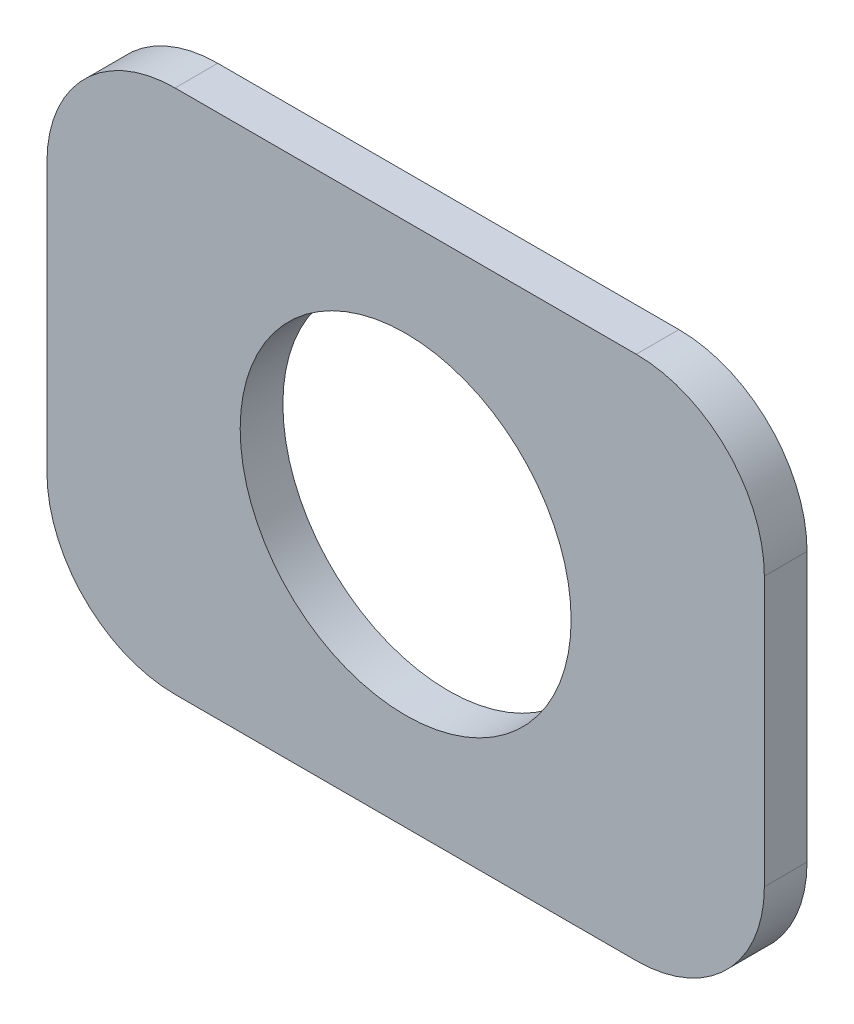
SolidWorks part; units mm, degrees
ref_plane "Front Plane" through (0, 0, 0) normal (0, 0, 1) x (1, 0, 0)
ref_plane "Top Plane" through (0, 0, 0) normal (0, 1, 0) x (1, 0, 0)
ref_plane "Right Plane" through (0, 0, 0) normal (1, 0, 0) x (0, 0, -1)
sketch "Sketch1" plane through (0, 0, 0) normal (0, 0, 1) x (1, 0, 0)
  line L0 (-4.2672, 1.6002) -> (-4.2672, -1.6002)
  line L1 (-2.7432, -3.1242) -> (2.7432, -3.1242)
  line L2 (4.2672, -1.6002) -> (4.2672, 1.6002)
  line L3 (2.7432, 3.1242) -> (-2.7432, 3.1242)
  circle A0 centre (0, 0) radius 1.9685
  arc A1 (-4.2672, -1.6002) -> (-2.7432, -3.1242) centre (-2.7432, -1.6002) ccw
  arc A2 (2.7432, -3.1242) -> (4.2672, -1.6002) centre (2.7432, -1.6002) ccw
  arc A3 (4.2672, 1.6002) -> (2.7432, 3.1242) centre (2.7432, 1.6002) ccw
  arc A4 (-2.7432, 3.1242) -> (-4.2672, 1.6002) centre (-2.7432, 1.6002) ccw
extrude "Boss-Extrude1" add sketch "Sketch1" along normal blind 0.508
